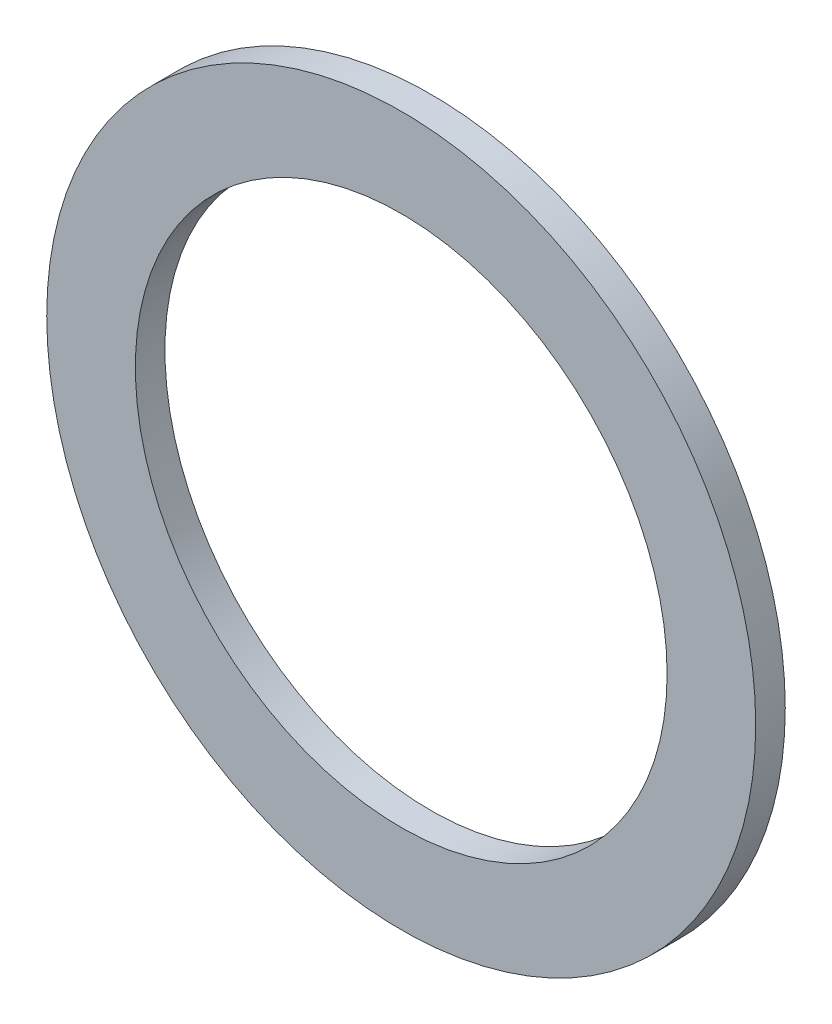
SolidWorks part; units mm, degrees
ref_plane "Front Plane" through (0, 0, 0) normal (0, 0, 1) x (1, 0, 0)
ref_plane "Top Plane" through (0, 0, 0) normal (0, 1, 0) x (1, 0, 0)
ref_plane "Right Plane" through (0, 0, 0) normal (1, 0, 0) x (0, 0, -1)
sketch "Sketch1" plane through (0, 0, 0) normal (0, 0, 1) x (1, 0, 0)
  circle A0 centre (0, 0) radius 38.1
  circle A1 centre (0, 0) radius 28.575
  dimension "D1" = 57.15
  dimension "D2" = 76.2
extrude "Boss-Extrude1" add sketch "Sketch1" along normal blind 3.175
equation "\"AIRFRAME_OD\"= 3.091in"
equation "\"AIRFRAME_ID\"= 3.00in"
equation "\"FLAT_T\"= 0.125in"
equation "\"COUPLER_OD\"= 2.998in"
equation "\"COUPLER_ID\"= 2.875in"
equation "\"NOSE_EXP_L\"= 3.5in"
equation "\"NOSE_SHOULDER_L\"= 5in"
equation "\"MAIN_L\"= 30in"
equation "\"RECO_COUP_L\"= 6in"
equation "\"RECO_SWITCH_L\"= 1.5in"
equation "\"RECO_ROD_X\"= 1.5in"
equation "\"DROGUE_L\"= 14in"
equation "\"ATS_FORE_COUP_L\"= 4in"
equation "\"ATS_AFT_COUP_L\"= 2.5in"
equation "\"ATS_ROD_X\"= 2in"
equation "\"LOWER_L\"= 16in"
equation "\"FIN_ROOT\"= 5in"
equation "\"FIN_X\"= 0.75in"
equation "\"FIN_N\"= 4"
equation "\"MOTOR_OD\"= 2.25in"
equation "\"MOTOR_ID\"= 2.126in"
equation "\"MOTOR_L\"= 8in"
equation "\"CR_AFT_X\"= 0.5in"
equation "\"CR_FORE_X\"= 6in"
equation "\"D1@Boss-Extrude1\"=\"FLAT_T\""
equation "\"D1@Sketch1\"=\"MOTOR_OD\""
equation "\"D2@Sketch1\"=\"AIRFRAME_ID\""
